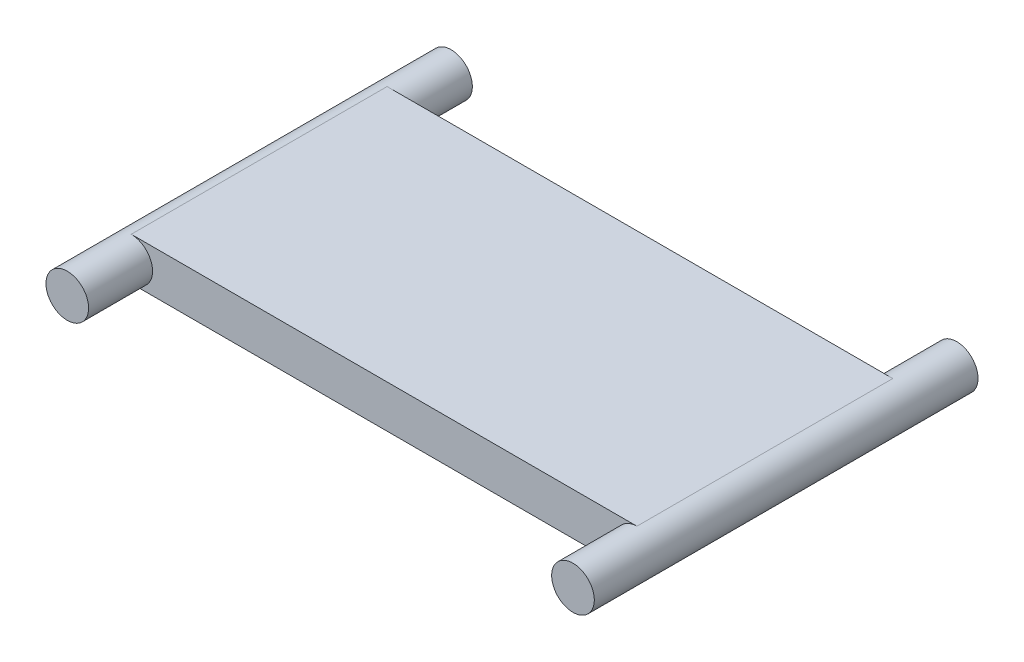
SolidWorks part; units mm, degrees
ref_plane "Front Plane" through (0, 0, 0) normal (0, 0, 1) x (1, 0, 0)
ref_plane "Top Plane" through (0, 0, 0) normal (0, 1, 0) x (1, 0, 0)
ref_plane "Right Plane" through (0, 0, 0) normal (1, 0, 0) x (0, 0, -1)
sketch "Sketch1" plane through (0, 0, 0) normal (0, 0, 1) x (1, 0, 0)
  line L2 (-18.8277, 1.5875) -> (18.8277, 1.5875)
  line L4 (-18.8277, -1.5875) -> (18.8277, -1.5875)
  line L6 (-18.8277, 1.5875) -> (18.8277, -1.5875) construction
  line L7 (-18.8277, -1.5875) -> (18.8277, 1.5875) construction
  arc A0 (-18.8277, 1.5875) -> (-18.8277, -1.5875) centre (-18.8277, 0) ccw
  arc A1 (18.8277, -1.5875) -> (18.8277, 1.5875) centre (18.8277, 0) ccw
  dimension "D3" = 1.5875
  dimension "D1" = 3.175
  dimension "D2" = 37.6555
extrude "Boss-Extrude1" add sketch "Sketch1" along normal mid plane 19.05
sketch "Sketch3" plane through (0, 0, 9.525) normal (0, 0, 1) x (1, 0, 0)
  circle A0 centre (-18.8277, 0) radius 1.5875
  arc A1 (-18.8277, 1.5875) -> (-18.8277, -1.5875) centre (-18.8277, 0) ccw construction
extrude "Boss-Extrude3" add sketch "Sketch3" along normal blind 4.7625
mirror "Mirror1" about plane through (0, 0, 0) normal (1, 0, 0) of "Boss-Extrude3"
mirror "Mirror2" about plane through (0, 0, 0) normal (0, 0, 1) of "Mirror1", "Boss-Extrude3"
